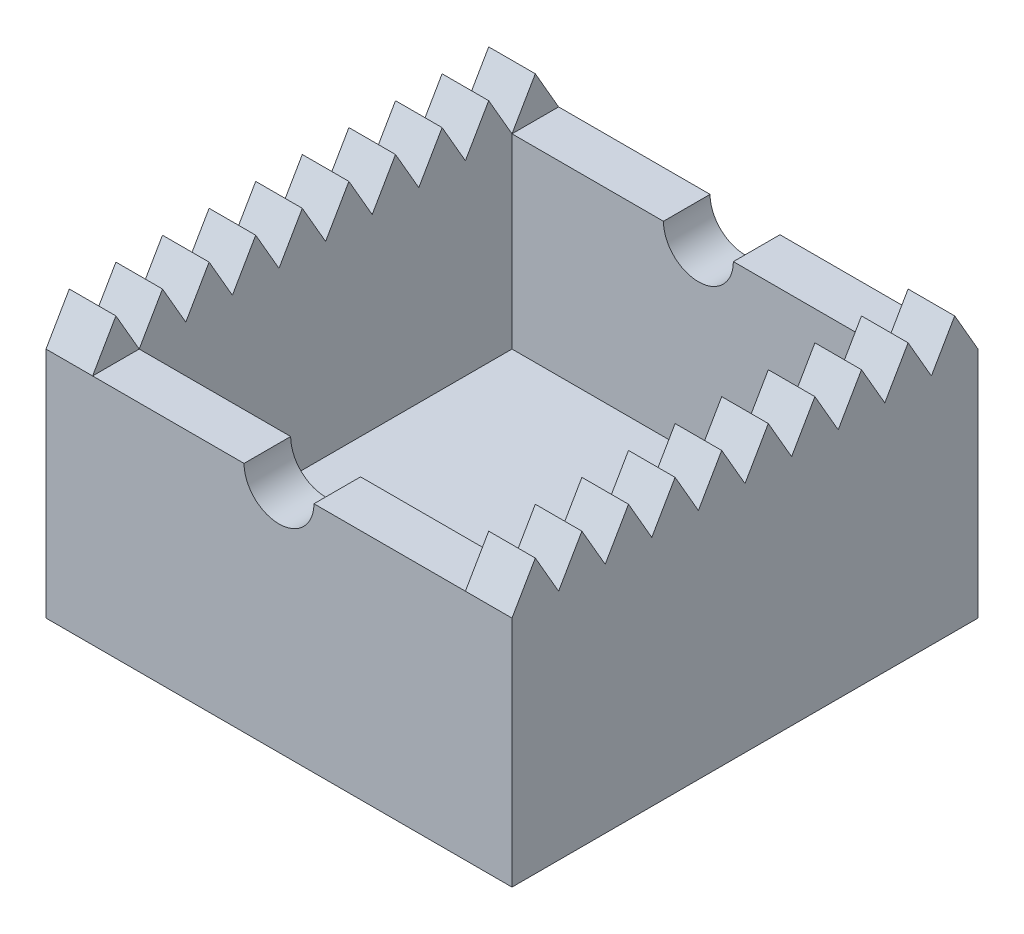
SolidWorks part; units mm, degrees
ref_plane "Front Plane" through (0, 0, 0) normal (0, 0, 1) x (1, 0, 0)
ref_plane "Top Plane" through (0, 0, 0) normal (0, 1, 0) x (1, 0, 0)
ref_plane "Right Plane" through (0, 0, 0) normal (1, 0, 0) x (0, 0, -1)
sketch "Sketch1" plane through (0, 0, 0) normal (0, 1, 0) x (1, 0, 0)
  line L1 (-50, -50) -> (50, -50)
  line L2 (-50, -50) -> (-50, 50)
  line L3 (-50, 50) -> (50, 50)
  line L4 (50, -50) -> (50, 50)
  line L5 (-50, -50) -> (50, 50) construction
  line L6 (-50, 50) -> (50, -50) construction
  line L11 (-40, -40) -> (40, 40) construction
  line L12 (-40, 40) -> (40, -40) construction
  point P0 (0, 0)
  point P6 (0, 0)
  dimension "D1" = 100
extrude "Boss-Extrude1" add sketch "Sketch1" along normal mid plane 50
sketch "Sketch4" plane through (0, 25, 0) normal (0, 1, 0) x (1, 0, 0)
  line L0 (50, 50) -> (-50, 50) construction
  line L1 (-40, -40) -> (40, -40)
  line L2 (-40, -40) -> (-40, 40)
  line L3 (-40, 40) -> (40, 40)
  line L4 (40, -40) -> (40, 40)
  line L5 (-40, -40) -> (40, 40) construction
  line L6 (-40, 40) -> (40, -40) construction
  point P0 (0, 0)
  dimension "D1" = 10
extrude "Cut-Extrude2" cut sketch "Sketch4" against normal offset from surface (40 mm away) 10 from surface at 0 up to face at (0, -25, 0) starting at face at (0, 25, 0)
sketch "Sketch5" plane through (0, 0, 50) normal (0, 0, 1) x (1, 0, 0)
  line L0 (-50, 25) -> (50, 25) construction
  circle A0 centre (0, 25) radius 7.5
  dimension "D1" = 15
extrude "Cut-Extrude3" cut sketch "Sketch5" against normal up to surface (100 mm away) from surface at 0 up to face at (0, 0, -50) starting at face at (0, 0, 50)
sketch "Sketch7" plane through (-50, 0, 0) normal (-1, 0, 0) x (0, 0, 1)
  line L0 (-50, 25) -> (-45, 33.6603)
  line L1 (-45, 33.6603) -> (-40, 25)
  line L2 (-50, 25) -> (50, 25) construction
  line L3 (-40, 25) -> (-50, 25)
  line L4 (-35, 33.6603) -> (-30, 25)
  line L5 (-40, 25) -> (-35, 33.6603)
  line L6 (-30, 25) -> (-40, 25)
  line L7 (-25, 33.6603) -> (-20, 25)
  line L8 (-30, 25) -> (-25, 33.6603)
  line L9 (-20, 25) -> (-30, 25)
  line L10 (-15, 33.6603) -> (-10, 25)
  line L11 (-20, 25) -> (-15, 33.6603)
  line L12 (-10, 25) -> (-20, 25)
  line L13 (-5, 33.6603) -> (0, 25)
  line L14 (-10, 25) -> (-5, 33.6603)
  line L15 (0, 25) -> (-10, 25)
  line L16 (5, 33.6603) -> (10, 25)
  line L17 (0, 25) -> (5, 33.6603)
  line L18 (10, 25) -> (0, 25)
  line L19 (15, 33.6603) -> (20, 25)
  line L20 (10, 25) -> (15, 33.6603)
  line L21 (20, 25) -> (10, 25)
  line L22 (25, 33.6603) -> (30, 25)
  line L23 (20, 25) -> (25, 33.6603)
  line L24 (30, 25) -> (20, 25)
  line L25 (35, 33.6603) -> (40, 25)
  line L26 (30, 25) -> (35, 33.6603)
  line L27 (40, 25) -> (30, 25)
  line L28 (45, 33.6603) -> (50, 25)
  line L29 (40, 25) -> (45, 33.6603)
  line L30 (50, 25) -> (40, 25)
  point P3 (0, 0)
  point P7 (0, 0)
  point P35 (0, 0)
  point P36 (0, 0)
  point P37 (0, 0)
  line M30 (50, 25) -> (-50, 25)
  dimension "D1" = 10
  dimension "D2" = 10
extrude "Boss-Extrude4" add sketch "Sketch7" against normal up to surface (10 mm away) contours L1 L0 M30 | L5 L4 M30 | L8 L7 M30 | L11 L10 M30 | L14 L13 M30 | L17 L16 M30 | L20 L19 M30 | L23 L22 M30 | L26 L25 M30 | L29 L28 M30 up to face at (-40, 5, 0)
sketch "Sketch8" plane through (50, 0, 0) normal (1, 0, 0) x (0, 0, -1)
  line L0 (-50, 25) -> (-45, 33.6603)
  line L1 (-45, 33.6603) -> (-40, 25)
  line L2 (-40, 25) -> (-50, 25)
  line L3 (-30, 25) -> (-40, 25)
  line L4 (-40, 25) -> (-35, 33.6603)
  line L5 (-35, 33.6603) -> (-30, 25)
  line L6 (-20, 25) -> (-30, 25)
  line L7 (-30, 25) -> (-25, 33.6603)
  line L8 (-25, 33.6603) -> (-20, 25)
  line L9 (-10, 25) -> (-20, 25)
  line L10 (-20, 25) -> (-15, 33.6603)
  line L11 (-15, 33.6603) -> (-10, 25)
  line L12 (0, 25) -> (-10, 25)
  line L13 (-10, 25) -> (-5, 33.6603)
  line L14 (-5, 33.6603) -> (0, 25)
  line L15 (10, 25) -> (0, 25)
  line L16 (0, 25) -> (5, 33.6603)
  line L17 (5, 33.6603) -> (10, 25)
  line L18 (20, 25) -> (10, 25)
  line L19 (10, 25) -> (15, 33.6603)
  line L20 (15, 33.6603) -> (20, 25)
  line L21 (30, 25) -> (20, 25)
  line L22 (20, 25) -> (25, 33.6603)
  line L23 (25, 33.6603) -> (30, 25)
  line L24 (40, 25) -> (30, 25)
  line L25 (30, 25) -> (35, 33.6603)
  line L26 (35, 33.6603) -> (40, 25)
  line L27 (50, 25) -> (40, 25)
  line L28 (40, 25) -> (45, 33.6603)
  line L29 (45, 33.6603) -> (50, 25)
  point P7 (0, 0)
  line M33 (50, 25) -> (-50, 25)
  dimension "D1" = 10
extrude "Boss-Extrude5" add sketch "Sketch8" against normal up to surface (10 mm away) contours L1 L0 M33 | L5 L4 M33 | L8 L7 M33 | L11 L10 M33 | L14 L13 M33 | L17 L16 M33 | L20 L19 M33 | L23 L22 M33 | L26 L25 M33 | L27 L28 L29 up to face at (40, 5, 0)
